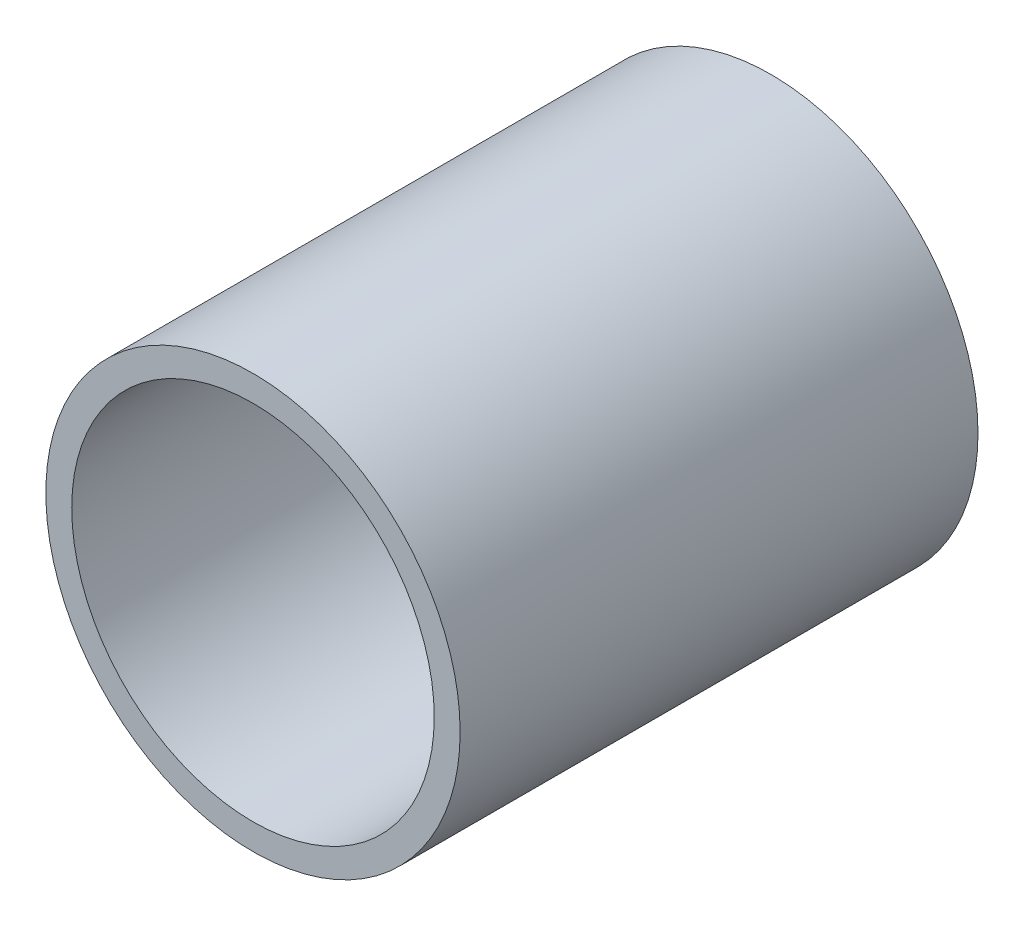
SolidWorks part; units mm, degrees
ref_plane "Front Plane" through (0, 0, 0) normal (0, 0, 1) x (1, 0, 0)
ref_plane "Top Plane" through (0, 0, 0) normal (0, 1, 0) x (1, 0, 0)
ref_plane "Right Plane" through (0, 0, 0) normal (1, 0, 0) x (0, 0, -1)
sketch "Sketch1" plane through (0, 0, 0) normal (0, 0, 1) x (1, 0, 0)
  circle A0 centre (0, 0) radius 4
  circle A1 centre (0, 0) radius 3.5
  dimension "D1" = 8
  dimension "D2" = 7
extrude "Boss-Extrude1" add sketch "Sketch1" along normal blind 10
